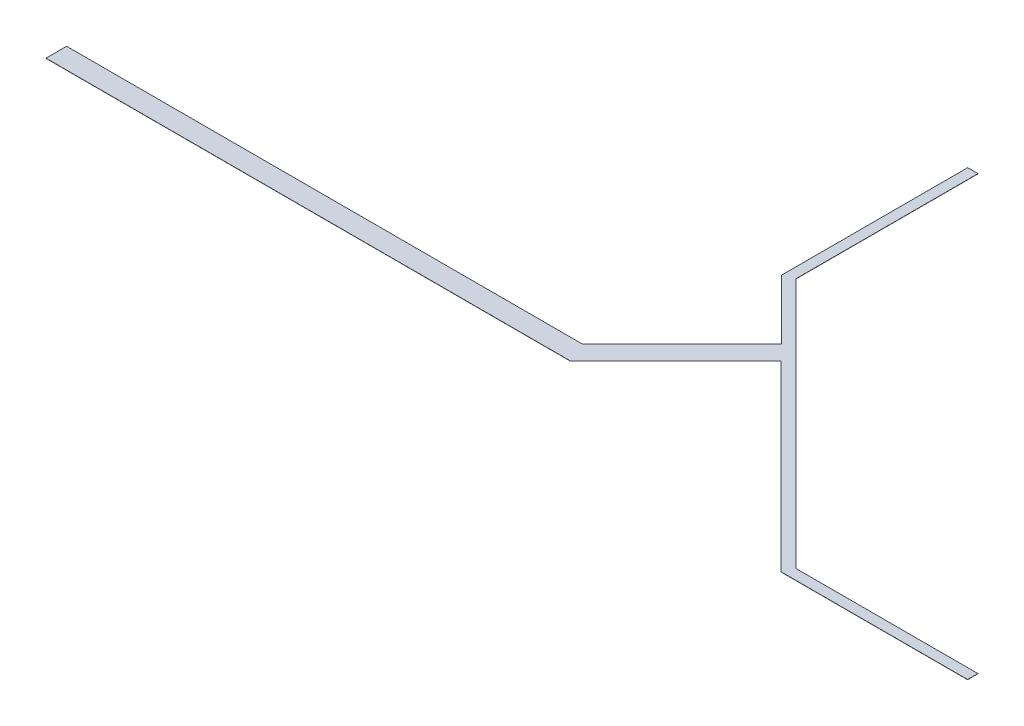
SolidWorks part; units mm, degrees
ref_plane "Front Plane" through (0, 0, 0) normal (0, 0, 1) x (1, 0, 0)
ref_plane "Top Plane" through (0, 0, 0) normal (0, 1, 0) x (1, 0, 0)
ref_plane "Right Plane" through (0, 0, 0) normal (1, 0, 0) x (0, 0, -1)
sketch "Sketch1" plane through (0, 0, 0) normal (0, 1, 0) x (1, 0, 0)
  line L0 (0, 0) -> (0, 2)
  line L1 (0, 0) -> (50.83, 0)
  line L2 (0, 2) -> (50, 2)
  line L3 (50, 2) -> (59.652, 11.652)
  line L4 (50.83, 0) -> (61.0618, 10.2318)
  line L5 (61.0618, 10.2318) -> (78.789, -7.4953)
  line L6 (59.652, 11.652) -> (53.8891, 17.4149)
  line L7 (78.789, -7.4953) -> (96.869, -7.4953)
  line L8 (53.8891, 17.4149) -> (53.8891, 35.4949)
  line L9 (53.8891, 35.4949) -> (54.8891, 35.4949)
  line L10 (96.869, -7.4953) -> (96.869, -6.4953)
  line L11 (96.869, -6.4953) -> (79.209, -6.4953)
  line L12 (54.8891, 35.4949) -> (54.8891, 17.8349)
  line L13 (54.8891, 17.8349) -> (79.209, -6.4953)
extrude "Boss-Extrude1" add sketch "Sketch1" along normal blind 0.02
scale "Scale2" scale about centroid uniform scaling yes scale factor 0.5
